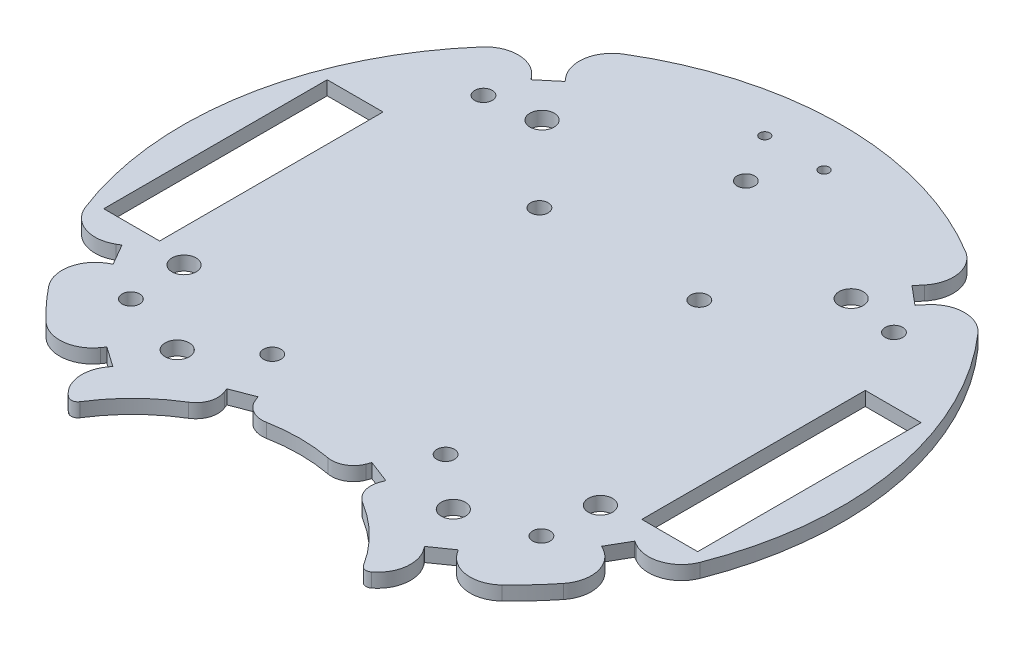
SolidWorks part; units mm, degrees
ref_plane "Front Plane" through (0, 0, 0) normal (0, 0, 1) x (1, 0, 0)
ref_plane "Top Plane" through (0, 0, 0) normal (0, 1, 0) x (1, 0, 0)
ref_plane "Right Plane" through (0, 0, 0) normal (1, 0, 0) x (0, 0, -1)
sketch "Sketch1" plane through (0, 0, 0) normal (0, 1, 0) x (1, 0, 0)
  line L0 (0, 0) -> (-32.9956, -67.352) construction
  line L1 (0, 86.2583) -> (0, -96.8543) construction
  line L2 (0, 0) -> (32.9956, -67.352) construction
  line L3 (-32.9956, -67.352) -> (0, -86.402) construction
  line L4 (32.9956, -67.352) -> (0, -86.402) construction
  line L5 (0, 0) -> (-13.6167, -50.8184) construction
  line L6 (0, 0) -> (-43.0182, -61.4364) construction
  line L7 (0, 0) -> (-48.2091, 57.4533) construction
  line L8 (-83.3992, 0) -> (107.0959, 0) construction
  line L9 (54.8141, -25.4) -> (54.8141, 25.4)
  line L10 (-67.5141, -25.4) -> (-54.8141, -25.4)
  line L11 (-67.5141, -25.4) -> (-67.5141, 25.4)
  line L12 (-67.5141, 25.4) -> (-54.8141, 25.4)
  line L13 (-54.8141, 25.4) -> (-54.8141, -25.4)
  line L14 (67.5141, 25.4) -> (54.8141, 25.4)
  line L15 (67.5141, -25.4) -> (67.5141, 25.4)
  line L16 (67.5141, -25.4) -> (54.8141, -25.4)
  line L17 (0, 0) -> (13.6167, -50.8184) construction
  line L18 (-64.9519, -37.5) -> (0, 0) construction
  line L19 (0, 0) -> (48.2091, 57.4533) construction
  line L20 (0, 0) -> (43.0182, -61.4364) construction
  line L21 (64.9519, -37.5) -> (0, 0) construction
  line L22 (-36.0148, -56.2289) -> (-35.4412, -55.4097)
  line L23 (12.5843, -45.8219) -> (12.9417, -44.8879)
  line L25 (-17.721, -47.7876) -> (-18.0784, -46.8536)
  line L26 (36.0148, -56.2289) -> (35.4412, -55.4097)
  line L27 (-59.1537, -30.9773) -> (-58.2877, -30.4773)
  line L28 (59.1537, -30.9773) -> (58.2877, -30.4773)
  line L29 (40.7784, 52.876) -> (39.4928, 51.3439)
  line L30 (-44.668, -58.998) -> (-44.6824, -59.0187)
  line L31 (-58.2877, -30.4773) -> (-55.5379, -35.24)
  line L32 (-35.4412, -55.4097) -> (-39.9465, -52.2551)
  line L33 (-40.7784, 52.876) -> (-40.1356, 52.11)
  line L34 (-55.5379, -35.24) -> (-56.404, -35.74)
  line L35 (-39.9465, -52.2551) -> (-40.5201, -53.0742)
  line L36 (-18.0784, -46.8536) -> (-12.9417, -44.8879)
  line L37 (-12.9417, -44.8879) -> (-12.5843, -45.8219)
  line L38 (12.9417, -44.8879) -> (18.0784, -46.8536)
  line L39 (18.0784, -46.8536) -> (17.721, -47.7876)
  line L40 (35.4412, -55.4097) -> (39.9465, -52.2551)
  line L41 (39.9465, -52.2551) -> (40.5201, -53.0742)
  line L42 (-13.6167, -50.8184) -> (-2.8571, -46.701) construction
  line L43 (58.2877, -30.4773) -> (55.5379, -35.24)
  line L44 (55.5379, -35.24) -> (56.404, -35.74)
  line L45 (-13.6167, -50.8184) -> (-17.7255, -40.0812) construction
  line L46 (39.4928, 51.3439) -> (43.706, 47.8086)
  line L47 (43.706, 47.8086) -> (44.9916, 49.3407)
  line L48 (-40.1356, 52.11) -> (-44.3488, 48.5746)
  line L49 (-44.3488, 48.5746) -> (-44.9916, 49.3407)
  arc A0 (-56.3744, 49.4664) -> (-69.893, -27.2023) centre (0, 0) ccw
  arc A1 (-19.7932, -53.8469) -> (-32.2407, -66.1006) centre (0, -86.402) ccw
  arc A2 (38.9256, 64.1077) -> (-38.9256, 64.1077) centre (0, 0) ccw
  arc A3 (56.3744, 49.4664) -> (44.9916, 49.3407) centre (50.737, 44.5198) ccw
  arc A4 (-56.3744, 49.4664) -> (-44.9916, 49.3407) centre (-50.737, 44.5198) cw
  arc A5 (-69.893, -27.2023) -> (-59.1537, -30.9773) centre (-62.9037, -24.4821) ccw
  arc A6 (-51.8486, -54.1915) -> (-40.5201, -53.0742) centre (-46.6637, -48.7724) ccw
  arc A7 (-38.9256, 64.1077) -> (-40.7784, 52.876) centre (-35.033, 57.6969) ccw
  arc A8 (-58.5044, -46.928) -> (-56.404, -35.74) centre (-52.654, -42.2352) cw
  arc A9 (-34.4197, -66.4939) -> (-36.0148, -56.2289) centre (-29.8711, -60.5307) cw
  arc A10 (38.9256, 64.1077) -> (40.7784, 52.876) centre (35.033, 57.6969) cw
  arc A11 (58.5044, -46.928) -> (56.404, -35.74) centre (52.654, -42.2352) ccw
  arc A12 (69.893, -27.2023) -> (59.1537, -30.9773) centre (62.9037, -24.4821) cw
  arc A13 (34.4197, -66.4939) -> (36.0148, -56.2289) centre (29.8711, -60.5307) ccw
  arc A14 (51.8486, -54.1915) -> (40.5201, -53.0742) centre (46.6637, -48.7724) cw
  arc A15 (-58.5044, -46.928) -> (-51.8486, -54.1915) centre (0, 0) ccw
  arc A16 (-33.1901, -67.2563) -> (-32.9956, -67.352) centre (0, 0) ccw
  arc A17 (51.8486, -54.1915) -> (58.5044, -46.928) centre (0, 0) ccw
  arc A18 (69.893, -27.2023) -> (56.3744, 49.4664) centre (0, 0) ccw
  arc A19 (-19.7932, -53.8469) -> (-17.721, -47.7876) centre (-22.3908, -49.5745) ccw
  arc A20 (-6.9964, -48.9499) -> (-12.5843, -45.8219) centre (-7.9145, -44.0349) cw
  arc A21 (19.7932, -53.8469) -> (17.721, -47.7876) centre (22.3908, -49.5745) cw
  arc A22 (6.9964, -48.9499) -> (12.5843, -45.8219) centre (7.9145, -44.0349) ccw
  arc A23 (6.9964, -48.9499) -> (-6.9964, -48.9499) centre (0, -86.402) ccw
  arc A24 (32.2407, -66.1006) -> (19.7932, -53.8469) centre (0, -86.402) ccw
  circle A25 centre (-18.179, 24.3106) radius 2
  circle A38 centre (-46.6637, -40.0812) radius 2
  circle A39 centre (46.6637, -40.0812) radius 2
  circle A40 centre (46.6637, 40.0812) radius 2
  circle A41 centre (-46.6637, 40.0812) radius 2
  arc A42 (-34.4197, -66.4939) -> (-32.2407, -66.1006) centre (-33.51, -65.3013) ccw
  arc A43 (34.4197, -66.4939) -> (32.2407, -66.1006) centre (33.51, -65.3013) cw
  circle A44 centre (-6.731, 64.1077) radius 1.143
  circle A45 centre (6.731, 64.1077) radius 1.143
  circle A46 centre (-31.3845, -44.8217) radius 2.75
  circle A47 centre (18.179, 24.3106) radius 2
  circle A48 centre (0, 53.0612) radius 2
  circle A49 centre (-47.3324, -27.3273) radius 2.75
  circle A50 centre (-35.1341, 41.8711) radius 2.75
  circle A51 centre (-19.7094, -34.8968) radius 2
  circle A52 centre (35.1341, 41.8711) radius 2.75
  circle A53 centre (47.3324, -27.3273) radius 2.75
  circle A54 centre (31.3845, -44.8217) radius 2.75
  circle A55 centre (19.7094, -34.8968) radius 2
  point P14 (-62.6039, 0)
  point P23 (62.6039, 0)
  point P35 (-31.3845, -44.8217)
  point P40 (-46.7211, -26.9744)
  point P45 (-34.6777, 41.3272)
  point P122 (-29.8711, 0)
  dimension "D1" = 150
  dimension "D3" = 120
  dimension "D2" = 76.2
  dimension "D11" = 1
  dimension "D15" = 13.462
  dimension "D18" = 2.286
  dimension "D12" = 4
  dimension "D4" = 50.8
  dimension "D5" = 12.7
  dimension "D6" = 80
  dimension "D7" = 80
  dimension "D8" = 25
  dimension "D9" = 30
extrude "Boss-Extrude1" add sketch "Sketch1" along normal blind 3.175
